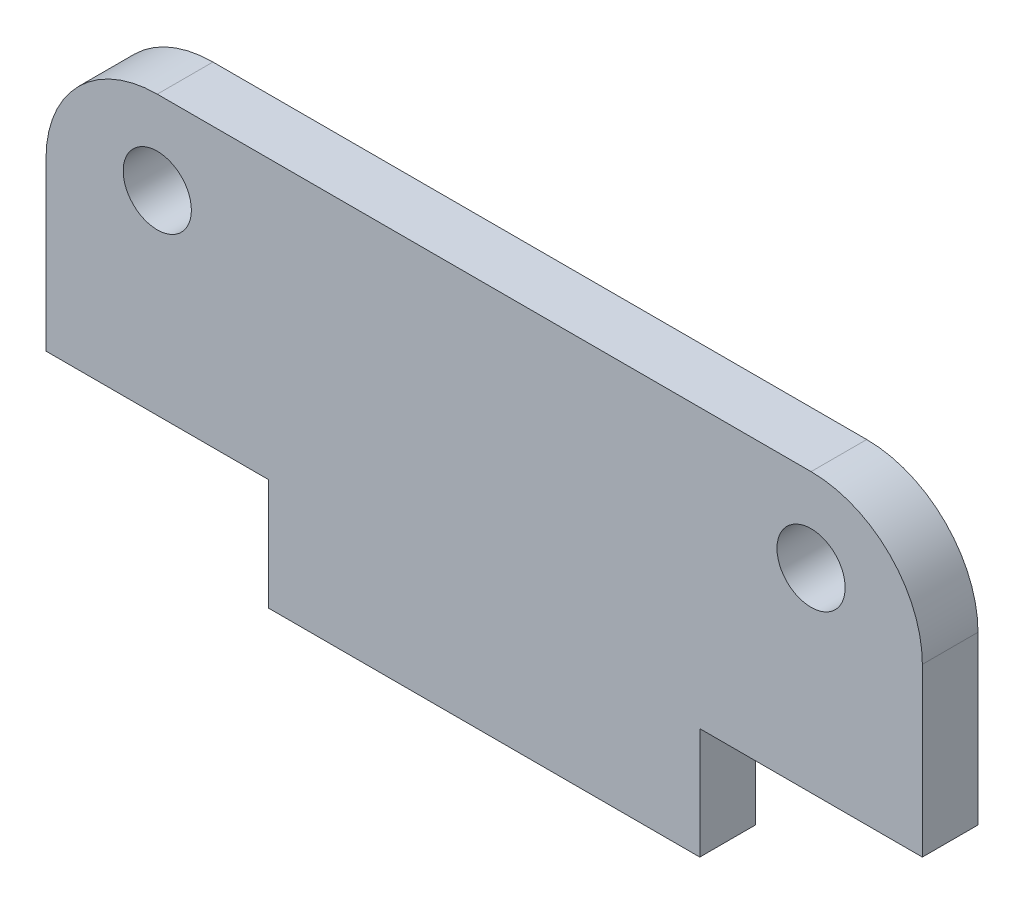
SolidWorks part; units mm, degrees
material "ABS"
ref_plane "Front Plane" through (0, 0, 0) normal (0, 0, 1) x (1, 0, 0)
ref_plane "Top Plane" through (0, 0, 0) normal (0, 1, 0) x (1, 0, 0)
ref_plane "Right Plane" through (0, 0, 0) normal (1, 0, 0) x (0, 0, -1)
sketch "Sketch1" plane through (0, 0, 0) normal (0, 0, 1) x (1, 0, 0)
  line L0 (-15.75, -7) -> (-7.75, -7)
  line L1 (-11.75, 3) -> (11.75, 3)
  line L2 (-15.75, -1) -> (-15.75, -7)
  line L3 (-7.75, -11) -> (7.75, -11)
  line L4 (7.75, -11) -> (7.75, -7)
  line L5 (15.75, -1) -> (15.75, -7)
  line L6 (-7.75, -11) -> (-7.75, -7)
  line L7 (0, 3) -> (0, -11) construction
  line L8 (15.75, -7) -> (7.75, -7)
  circle A0 centre (-11.75, 0) radius 1.225
  arc A1 (11.75, 3) -> (15.75, -1) centre (11.75, -1) cw
  circle A2 centre (11.75, 0) radius 1.225
  arc A3 (-11.75, 3) -> (-15.75, -1) centre (-11.75, -1) ccw
  dimension "D1" = 2.45
  dimension "D3" = 4
  dimension "D2" = 11.75
  dimension "D4" = 1
  dimension "D5" = 15.75
  dimension "D6" = 7.75
  dimension "D7" = 4
  dimension "D8" = 14
extrude "Main Body" add sketch "Sketch1" along normal blind 2
equation "\"D1@Sketch1\"=2.00mm+\"print_free@Parameters@RobotHandParameters.SLDPRT\""
